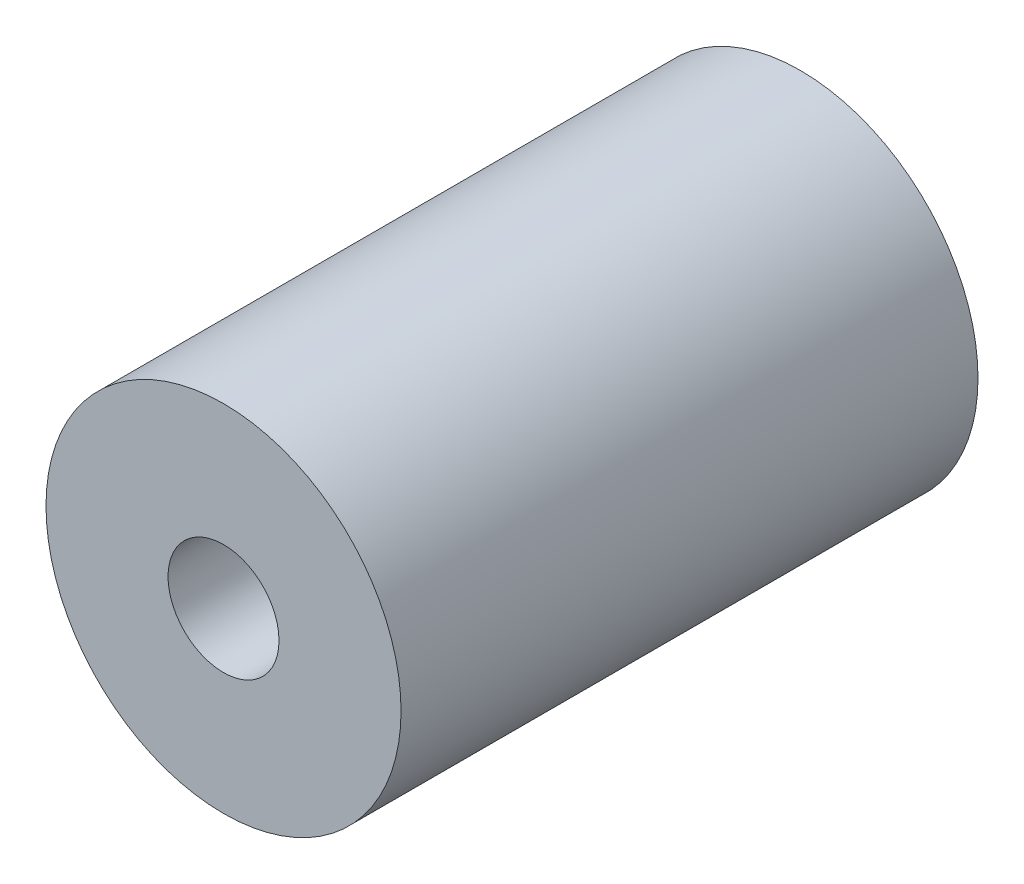
SolidWorks part; units mm, degrees
ref_plane "Front Plane" through (0, 0, 0) normal (0, 0, 1) x (1, 0, 0)
ref_plane "Top Plane" through (0, 0, 0) normal (0, 1, 0) x (1, 0, 0)
ref_plane "Right Plane" through (0, 0, 0) normal (1, 0, 0) x (0, 0, -1)
sketch "Sketch1" plane through (0, 0, 0) normal (0, 0, 1) x (1, 0, 0)
  circle A0 centre (0, 0) radius 8
  circle A1 centre (0, 0) radius 2.5
  dimension "D1" = 16
  dimension "D2" = 5
extrude "Boss-Extrude1" add sketch "Sketch1" along normal blind 26
ref_plane "Plane1" through (0, 0, 18) normal (0, 0, 1) x (1, 0, 0)
sketch "Sketch2" plane through (0, 0, 18) normal (0, 0, 1) x (1, 0, 0)
  circle A0 centre (0, 0) radius 3.5
  dimension "D1" = 7
extrude "Cut-Extrude1" cut sketch "Sketch2" against normal blind 10
